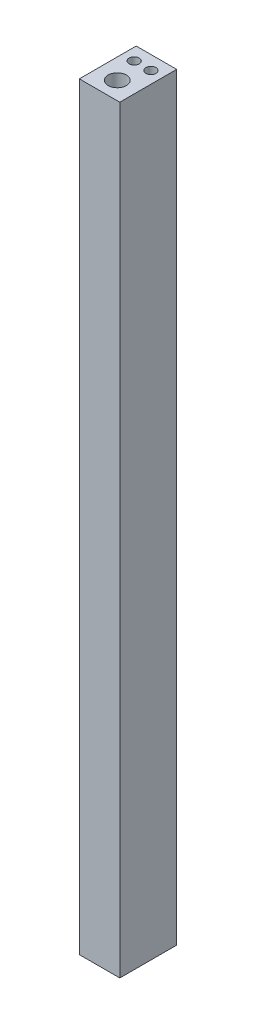
SolidWorks part; units mm, degrees
ref_plane "Front Plane" through (0, 0, 0) normal (0, 0, 1) x (1, 0, 0)
ref_plane "Top Plane" through (0, 0, 0) normal (0, 1, 0) x (1, 0, 0)
ref_plane "Right Plane" through (0, 0, 0) normal (1, 0, 0) x (0, 0, -1)
sketch "Sketch2" plane through (0, 0, 0) normal (0, 1, 0) x (1, 0, 0)
  line L1 (-1.6, 2.25) -> (1.6, 2.25)
  line L2 (-1.6, 2.25) -> (-1.6, -2.25)
  line L3 (-1.6, -2.25) -> (1.6, -2.25)
  line L4 (1.6, 2.25) -> (1.6, -2.25)
  line L5 (-1.6, 2.25) -> (1.6, -2.25) construction
  line L6 (-1.6, -2.25) -> (1.6, 2.25) construction
  point P0 (0, 0)
  dimension "D1" = 3.2
  dimension "D2" = 4.5
extrude "Boss-Extrude1" add sketch "Sketch2" along normal blind 60
sketch "Sketch5" plane through (0, 60, 0) normal (0, 1, 0) x (-1, 0, 0)
  circle A0 centre (0, 0.8496) radius 0.725
  dimension "D1" = 1.45
extrude "Cut-Extrude1" cut sketch "Sketch5" against normal through all
sketch "Sketch6" plane through (0, 60, 0) normal (0, 1, 0) x (-1, 0, 0)
  circle A0 centre (0.6569, -1.1451) radius 0.4
  circle A1 centre (0, 0.8496) radius 0.725 construction
  dimension "D1" = 0.8
  dimension "D2" = 2.1
extrude "Cut-Extrude2" cut sketch "Sketch6" against normal through all
sketch "Sketch7" plane through (0, 60, 0) normal (0, 1, 0) x (-1, 0, 0)
  circle A0 centre (-0.658, -1.1533) radius 0.4
  circle A3 centre (0, 0.8496) radius 0.725 construction
  dimension "D1" = 0.8
  dimension "D2" = 2.1082
extrude "Cut-Extrude3" cut sketch "Sketch7" against normal through all
